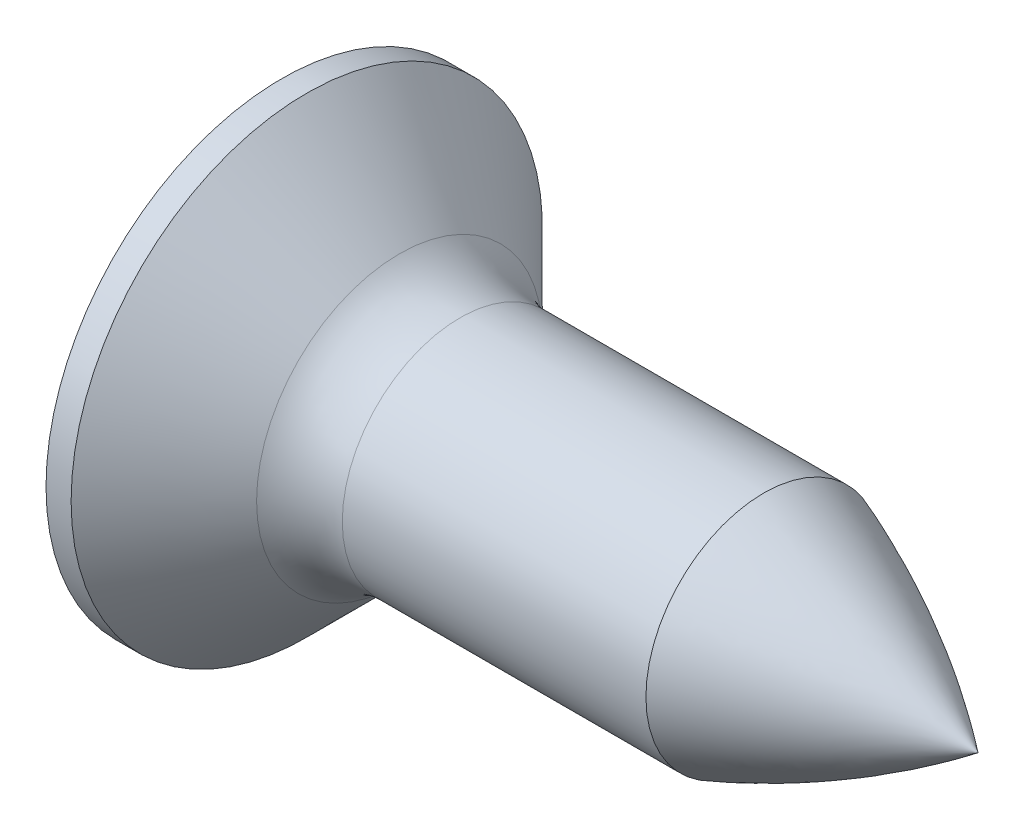
SolidWorks part; units mm, degrees
ref_plane "Front" through (0, 0, 0) normal (0, 0, 1) x (1, 0, 0)
ref_plane "Top" through (0, 0, 0) normal (0, 1, 0) x (1, 0, 0)
ref_plane "Right" through (0, 0, 0) normal (1, 0, 0) x (0, 0, -1)
sketch "Sketch1" plane through (0, 0, 0) normal (0, 0, 1) x (1, 0, 0)
  line L0 (-20.4182, 0) -> (11.3165, 0) construction
  line L1 (7, 0) -> (7, 1.1)
  line L2 (7, 1.1) -> (2.1657, 1.1)
  line L3 (2.4, 2.2) -> (2.4, -0.8442) construction
  line L4 (0.7343, 2.2) -> (0.5, 2.2)
  line L5 (7, 0) -> (0, 0)
  line L6 (1.6, 1.3343) -> (0.7343, 2.2)
  arc A0 (0.5, 2.2) -> (0, 0) centre (5.09, 0) ccw
  arc A1 (2.1657, 1.1) -> (1.6, 1.3343) centre (2.1657, 1.9) cw
  dimension "r" = 0.8
  dimension "st" = 2.2
  dimension "dk" = 4.4
  dimension "l" = 6.5
  dimension "f" = 0.5
  dimension "D2" = 45
  dimension "k" = 1.1
  dimension "a" = 0.8
revolve "Base" add sketch "Sketch1" angle 360 about L0
cosmetic thread "ThreadCosmetic1" [suppressed] parameters "D1"=4.6, "D2"=1.2
sketch "Sketch2" plane through (0, 0, 0) normal (1, 0, 0) x (0, 0, -1)
  line L0 (6.5369, 0) -> (-7.0008, 0) construction
  line L1 (0, 6.811) -> (0, -6.4314) construction
  line L2 (-0.22, 1.1) -> (0.22, 1.1)
  line L3 (0.22, 1.1) -> (0.22, 0.22)
  line L4 (0.22, 0.22) -> (1.1, 0.22)
  line L5 (1.1, 0.22) -> (1.1, -0.22)
  line L6 (0.22, -0.22) -> (1.1, -0.22)
  line L7 (0.22, -1.1) -> (0.22, -0.22)
  line L8 (-0.22, -1.1) -> (0.22, -1.1)
  line L9 (-0.22, -1.1) -> (-0.22, -0.22)
  line L10 (-0.22, -0.22) -> (-1.1, -0.22)
  line L11 (-1.1, 0.22) -> (-1.1, -0.22)
  line L12 (-0.22, 0.22) -> (-1.1, 0.22)
  line L13 (-0.22, 1.1) -> (-0.22, 0.22)
  point P5 (-1.1, 0)
  point P11 (1.1, 0)
  point P15 (0, -1.1)
  point P20 (0, 1.1)
  dimension "m" = 2.2
  dimension "D2" = 2.2
  dimension "D3" = 0.44
  dimension "D4" = 0.44
extrude "CrossRecess" cut sketch "Sketch2" along normal blind 1.2
sketch "Sketch3" plane through (0, 0, 0) normal (1, 0, 0) x (0, 0, -1)
  line L0 (-4.5467, 4.5467) -> (4.5467, -4.5467) construction
  line L1 (-0.9538, 0.9538) -> (-0.22, 0.44)
  line L3 (-0.22, 0.44) -> (-0.22, 0.22)
  line L4 (-0.44, 0.22) -> (-0.22, 0.22)
  line L5 (-0.9538, 0.9538) -> (-0.44, 0.22)
  line L6 (7.069, 0) -> (-6.5067, 0) construction
  line L7 (0, 5.9645) -> (0, -0.3816) construction
  line L8 (0.9538, 0.9538) -> (0.44, 0.22)
  line L9 (0.44, 0.22) -> (0.22, 0.22)
  line L10 (0.22, 0.44) -> (0.22, 0.22)
  line L11 (0.9538, 0.9538) -> (0.22, 0.44)
  line L12 (0.9538, -0.9538) -> (0.22, -0.44)
  line L13 (0.22, -0.44) -> (0.22, -0.22)
  line L14 (0.44, -0.22) -> (0.22, -0.22)
  line L15 (0.9538, -0.9538) -> (0.44, -0.22)
  line L16 (-0.9538, -0.9538) -> (-0.44, -0.22)
  line L17 (-0.44, -0.22) -> (-0.22, -0.22)
  line L18 (-0.22, -0.44) -> (-0.22, -0.22)
  line L19 (-0.9538, -0.9538) -> (-0.22, -0.44)
  line L21 (0.22, 0.22) -> (1.1, 0.22) construction
  line L22 (0.22, 1.1) -> (0.22, 0.22) construction
  dimension "D1" = 20
  dimension "D2" = 0.22
extrude "Cut-Extrude2" [suppressed] cut sketch "Sketch3" along normal up to surface (2.25 mm away)
sketch "Sketch4" plane through (0, 0, 0) normal (0, 0, 1) x (1, 0, 0)
  line L0 (35.6282, 0) -> (20.6612, 0) construction
  line L2 (5.4, -1.1) -> (6.2, -1.1)
  line L3 (6.2, -1.1) -> (7, -0.9)
  line L5 (7, -1.1) -> (7, 1.1) construction
  line L6 (5.4, -1.1) -> (5.4, -1.6)
  line L7 (5.4, -1.6) -> (7, -1.6)
  line L8 (7, -1.6) -> (7, -0.9)
  point P15 (6.2, -1.1)
  dimension "yf" = 1.6
  dimension "D2" = 0.8
  dimension "D1" = 2.2
  dimension "D3" = 0.2
  dimension "D4" = 0.5
revolve "Cut-Revolve1" [suppressed] cut sketch "Sketch4" angle 360 about L0
sketch "Sketch5" plane through (0, 0, 0) normal (0, 0, 1) x (1, 0, 0)
  line L0 (37.0407, 0) -> (13.7121, 0) construction
  line L2 (7, -1.1) -> (7, 1.1) construction
  line L3 (7, 0) -> (5, -1.1) construction
  line L6 (7, 0) -> (7.5, 0)
  line L7 (5, -1.1) -> (7, -1.1)
  line L8 (7.5, 0) -> (7.5, -1.1)
  line L9 (7.5, -1.1) -> (7, -1.1)
  arc A0 (7, 0) -> (5, -1.1) centre (2.1841, 6.388) cw
  dimension "D1" = 8
  dimension "yc" = 2
  dimension "D3" = 2.2
  dimension "D2" = 0.5
revolve "Cut-Revolve6" cut sketch "Sketch5" angle 360 about L0
draft "Draft1" type of draft neutral plane draft angle 30 neutral plane "Right" faces to draft 4 face at (0.6614, -1.1, 0) face at (0.6614, 0, -1.1) face at (0.6614, 0, 1.1) face at (0.6614, 1.1, 0) neutral plane through (0, 0, 0) neutral plane normal (1, 0, 0) reverse direction yes parameters "D1"=30
sketch "Sketch6" plane through (0, 0, 0) normal (0, 0, 1) x (1, 0, 0)
  line L0 (2.15, 1.6) -> (2.65, 1.6)
  line L1 (2.65, 1.6) -> (2.65, 1.1)
  line L2 (2.65, 1.1) -> (2.4, 0.667)
  line L3 (2.4, 0.667) -> (2.15, 1.1)
  line L4 (2.15, 1.1) -> (2.15, 1.6)
  line L5 (0, 0) -> (5.4654, 0) construction
  dimension "D1" = 2.2
  dimension "D2" = 0.5
  dimension "D3" = 0.8
revolve "Cut-Revolve10" [suppressed] cut sketch "Sketch6" angle 360 about L5
pattern_linear "LPattern10" [suppressed] count 8 spacing 0.6 along (1, 0, 0)
equation "\"D3@Sketch2\" = \"m@Sketch2\" / 5"
equation "\"D4@Sketch2\" = \"D3@Sketch2\""
equation "\"D2@Sketch2\" = \"m@Sketch2\""
equation "\"D2@Sketch3\" = \"m@Sketch2\" / 10"
equation "\"D3@Sketch4\" = \"yf@Sketch4\" / 8"
equation "\"D2@ThreadCosmetic1\" = \"st@Sketch1\" - 1"
equation "\"D1@Sketch5\" = \"yc@Sketch5\" * 4"
equation "\"D3@Sketch5\" = \"st@Sketch1\""
equation "\"D2@Sketch4\" = \"yf@Sketch4\" / 2"
equation "\"D1@Sketch4\" = \"st@Sketch1\""
equation "\"D1@ThreadCosmetic1\" = \"l@Sketch1\" - \"k@Sketch1\" - \"a@Sketch1\""
equation "\"D1@Sketch6\" = \"st@Sketch1\""
equation "\"D2@Sketch6\" =  ( \"D1@Sketch6\" - \"D2@ThreadCosmetic1\" )  / 2"
equation "\"D3@Sketch6\" = \"a@Sketch1\""
equation "\"D3@LPattern10\" = \"D2@Sketch6\" * 1.2"
equation "\"D1@LPattern10\" = \"D1@ThreadCosmetic1\" / \"D3@LPattern10\""
